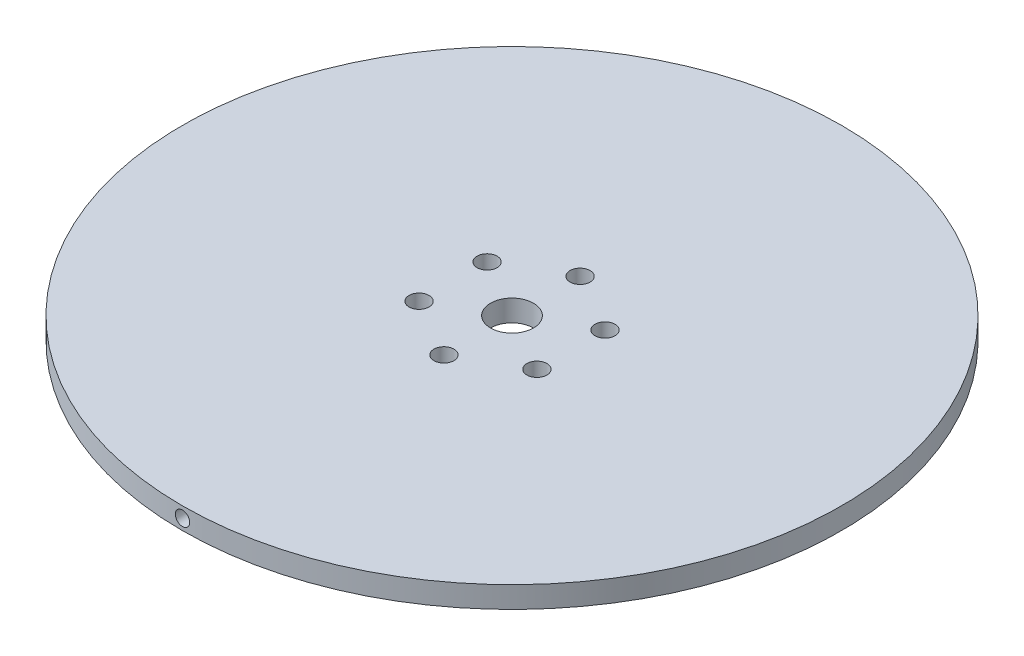
SolidWorks part; units mm, degrees
material "1060 Alloy"
ref_plane "Front Plane" through (0, 0, 0) normal (0, 0, 1) x (1, 0, 0)
ref_plane "Top Plane" through (0, 0, 0) normal (0, 1, 0) x (1, 0, 0)
ref_plane "Right Plane" through (0, 0, 0) normal (1, 0, 0) x (0, 0, -1)
sketch "Sketch1" plane through (0, 0, 0) normal (0, 1, 0) x (1, 0, 0)
  circle A0 centre (0, 0) radius 46
  circle A1 centre (0, 0) radius 3
  circle A3 centre (0, 9.5) radius 1.4
  circle A4 centre (8.2272, 4.75) radius 1.4
  circle A5 centre (8.2272, -4.75) radius 1.4
  circle A6 centre (0, -9.5) radius 1.4
  circle A7 centre (-8.2272, -4.75) radius 1.4
  circle A8 centre (-8.2272, 4.75) radius 1.4
  point P20 (0, 0)
  dimension "D1" = 92
  dimension "D2" = 6
  dimension "D4" = 2.8
  dimension "D5" = 6
extrude "Boss-Extrude1" add sketch "Sketch1" along normal blind 3
ref_plane "Plane2" through (0, 0, 46) normal (0, 0, 1) x (1, 0, 0)
sketch "Sketch5" plane through (0, 0, 46) normal (0, 0, 1) x (1, 0, 0)
  line L0 (0, 0) -> (0, 1.5) construction
  circle A0 centre (0, 1.5) radius 1
  dimension "D2" = 2
  dimension "D1" = 1.5
extrude "Cut-Extrude1" cut sketch "Sketch5" against normal blind 3
ref_plane "Plane3" through (0, 0, -46) normal (0, 0, 1) x (1, 0, 0)
sketch "Sketch6" plane through (0, 0, -46) normal (0, 0, 1) x (1, 0, 0)
  line L0 (0, 0) -> (0, 1.5) construction
  line L1 (-46, 0) -> (46, 0) construction
  circle A0 centre (0, 1.5) radius 1
  dimension "D2" = 2
  dimension "D1" = 1.5
extrude "Cut-Extrude2" cut sketch "Sketch6" along normal blind 3
